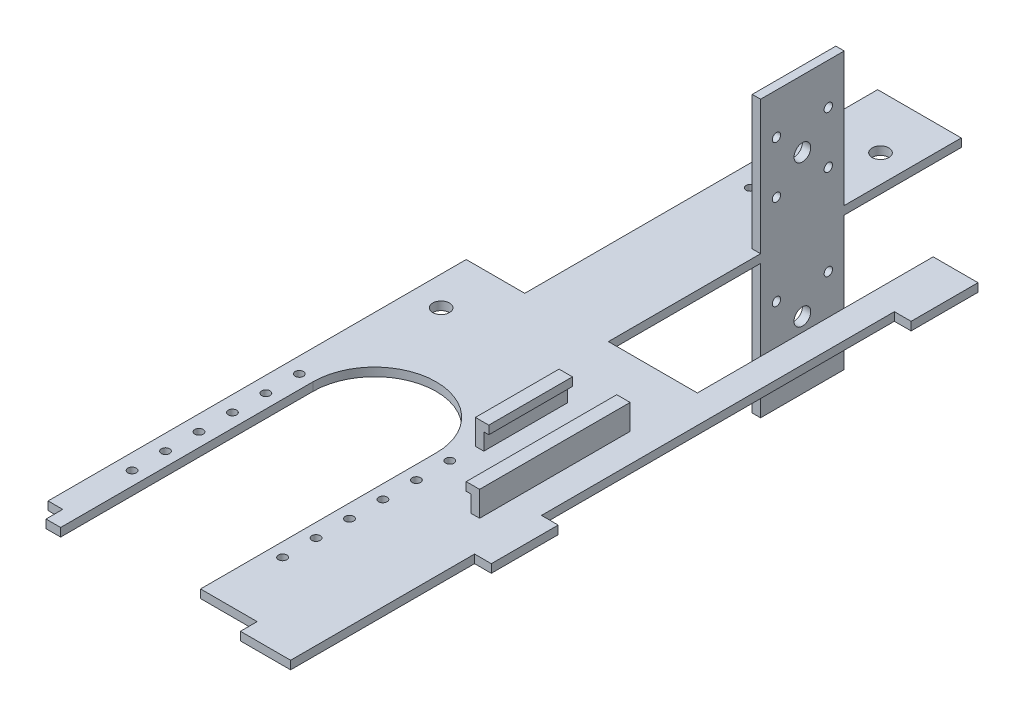
SolidWorks part; units mm, degrees
ref_plane "Front Plane" through (0, 0, 0) normal (0, 0, 1) x (1, 0, 0)
ref_plane "Top Plane" through (0, 0, 0) normal (0, 1, 0) x (1, 0, 0)
ref_plane "Right Plane" through (0, 0, 0) normal (1, 0, 0) x (0, 0, -1)
sketch "Sketch1" plane through (0, 0, 0) normal (0, 0, 1) x (1, 0, 0)
  line L1 (-30, 2.5) -> (30, 2.5)
  line L2 (-30, 2.5) -> (-30, -2.5)
  line L3 (-30, -2.5) -> (30, -2.5)
  line L4 (30, 2.5) -> (30, -2.5)
  line L5 (-30, 2.5) -> (30, -2.5) construction
  line L6 (-30, -2.5) -> (30, 2.5) construction
  point P0 (0, 0)
  dimension "D1" = 60
  dimension "D2" = 5
extrude "Boss-Extrude1" add sketch "Sketch1" along normal blind 391
sketch "Sketch3" plane through (-30, 0, 0) normal (-1, 0, 0) x (0, 0, 1)
  line L0 (391, -2.5) -> (0, -2.5) construction
  line L1 (391, -2.5) -> (141, -2.5)
  line L2 (391, -2.5) -> (391, 2.5)
  line L3 (391, 2.5) -> (141, 2.5)
  line L4 (141, -2.5) -> (141, 2.5)
  line L5 (391, 2.5) -> (391, -2.5) construction
  line L6 (391, 2.5) -> (0, 2.5) construction
  dimension "D1" = 250
extrude "Boss-Extrude2" add sketch "Sketch3" along normal blind 95
sketch "Sketch4" plane through (0, -2.5, 0) normal (0, -1, 0) x (1, 0, 0)
  line L0 (-70.67, 391) -> (-70.67, 250.12) construction
  line L4 (-125, 391) -> (30, 391) construction
  line L5 (-125, 141) -> (-125, 391) construction
  line L6 (-70.67, 391) -> (-70.67, 250.12) construction
  line L7 (-33.84, 391) -> (-33.84, 250.12)
  line L8 (-107.5, 391) -> (-107.5, 250.12)
  line L9 (-125, 250.12) -> (-11.4037, 250.12) construction
  arc A0 (-33.84, 391) -> (-107.5, 391) centre (-70.67, 391) ccw
  arc A1 (-107.5, 250.12) -> (-33.84, 250.12) centre (-70.67, 250.12) ccw
  circle A2 centre (-115.67, 250.12) radius 2.5
  circle A3 centre (-25.67, 250.12) radius 2.5
  circle A4 centre (-25.67, 270.12) radius 2.5
  circle A5 centre (-25.67, 290.12) radius 2.5
  circle A6 centre (-25.67, 310.12) radius 2.5
  circle A7 centre (-25.67, 330.12) radius 2.5
  circle A8 centre (-25.67, 350.12) radius 2.5
  circle A9 centre (-115.67, 270.12) radius 2.5
  circle A10 centre (-115.67, 290.12) radius 2.5
  circle A11 centre (-115.67, 310.12) radius 2.5
  circle A12 centre (-115.67, 330.12) radius 2.5
  circle A13 centre (-115.67, 350.12) radius 2.5
  point P6 (-70.67, 320.56)
  dimension "D3" = 36.83
  dimension "D4" = 5
  dimension "D1" = 54.33
  dimension "D2" = 140.88
  dimension "D5" = 45
  dimension "D8" = 45
  dimension "D6" = 2
  dimension "D7" = 6
extrude "Cut-Extrude1" cut sketch "Sketch4" against normal blind 95
sketch "Sketch5" plane through (0, -2.5, 0) normal (0, -1, 0) x (1, 0, 0)
  line L1 (-125, 141) -> (-30, 141) construction
  line L2 (-40, 141) -> (-90, 141)
  line L3 (-40, 141) -> (-40, 0)
  line L4 (-40, 0) -> (-90, 0)
  line L5 (-90, 141) -> (-90, 0)
  line L6 (-30, 141) -> (-30, 0) construction
  dimension "D1" = 50
  dimension "D2" = 10
extrude "Boss-Extrude3" add sketch "Sketch5" against normal blind 5
sketch "Sketch6" plane through (0, -2.5, 0) normal (0, -1, 0) x (1, 0, 0)
  line L0 (-90, 0) -> (-40, 0) construction
  line L1 (-40, 0) -> (-45, 0)
  line L2 (-40, 0) -> (-40, 50)
  line L3 (-40, 50) -> (-45, 50)
  line L4 (-45, 0) -> (-45, 50)
  line L6 (-40, 0) -> (-40, 141) construction
  dimension "D1" = 50
  dimension "D2" = 5
  dimension "D3" = 0
extrude "Boss-Extrude4" add sketch "Sketch6" along normal blind 80
sketch "Sketch7" plane through (-45, 0, 0) normal (-1, 0, 0) x (0, 0, 1)
  line L0 (50, -42.5) -> (0, -42.5) construction
  line L1 (50, -82.5) -> (50, -2.5) construction
  line L2 (0, -82.5) -> (0, -2.5) construction
  circle A0 centre (25, -42.5) radius 5
  dimension "D1" = 10
extrude "Cut-Extrude2" cut sketch "Sketch7" against normal blind 40
sketch "Sketch8" plane through (0, -2.5, 0) normal (0, -1, 0) x (-1, 0, 0)
  line L0 (30, -141) -> (30, 0) construction
  line L1 (30, -141) -> (0, -141)
  line L2 (30, -141) -> (30, 0)
  line L3 (30, 0) -> (0, 0)
  line L4 (0, -141) -> (-13.214, -141)
  line L5 (30, 0) -> (-30, 0) construction
  line L6 (-13.214, -141) -> (-13.214, 0)
  line L7 (-13.214, 0) -> (0, 0)
extrude "Cut-Extrude3" cut sketch "Sketch8" against normal blind 10
sketch "Sketch11" plane through (30, 0, 0) normal (1, 0, 0) x (0, 0, -1)
  line L0 (-391, -2.5) -> (0, -2.5) construction
  line L1 (0, 2.5) -> (-40, 2.5)
  line L2 (0, 2.5) -> (0, -2.5)
  line L3 (0, -2.5) -> (-40, -2.5)
  line L4 (-40, 2.5) -> (-40, -2.5)
  line L5 (-391, 2.5) -> (0, 2.5) construction
  line L6 (-251, -2.5) -> (-291, -2.5)
  line L7 (-251, -2.5) -> (-251, 2.5)
  line L8 (-251, 2.5) -> (-291, 2.5)
  line L9 (-291, -2.5) -> (-291, 2.5)
  dimension "D1" = 40
  dimension "D2" = 40
  dimension "D3" = 100
extrude "Boss-Extrude5" add sketch "Sketch11" along normal blind 10
sketch "Sketch12" plane through (0, 0, 391) normal (0, 0, 1) x (1, 0, 0)
  line L1 (-33.84, -2.5) -> (30, -2.5) construction
  line L2 (30, 2.5) -> (0, 2.5)
  line L3 (30, 2.5) -> (30, -2.5)
  line L4 (30, -2.5) -> (0, -2.5)
  line L5 (0, 2.5) -> (0, -2.5)
  line L6 (-107.5, -2.5) -> (-125, -2.5)
  line L7 (-107.5, -2.5) -> (-107.5, 2.5)
  line L8 (-107.5, 2.5) -> (-125, 2.5)
  line L9 (-125, -2.5) -> (-125, 2.5)
  dimension "D1" = 30
extrude "Boss-Extrude6" add sketch "Sketch12" along normal blind 10
mirror "Mirror1" about plane through (0, 0, 0) normal (0, 1, 0) of "Cut-Extrude2", "Boss-Extrude4"
ref_plane "Plane3" through (-107.5, 2.5, 401) normal (-1, 0, 0) x (0, 0, 1)
sketch "Sketch14" plane through (0, 0, 401) normal (0, 0, 1) x (1, 0, 0)
  line L0 (-125, -2.5) -> (-107.5, -2.5) construction
  line L1 (-125.25, -2.5) -> (-116.25, -2.5)
  line L2 (-125.25, -2.5) -> (-125.25, 2.5)
  line L3 (-125.25, 2.5) -> (-116.25, 2.5)
  line L4 (-116.25, -2.5) -> (-116.25, 2.5)
  line L5 (-107.5, 2.5) -> (-125, 2.5) construction
  dimension "D1" = 9
extrude "Cut-Extrude4" cut sketch "Sketch14" against normal blind 10
sketch "Sketch15" plane through (0, -2.5, 0) normal (0, -1, 0) x (1, 0, 0)
  line L0 (30, 251) -> (30, 40) construction
  line L1 (13, 271) -> (8, 271)
  line L2 (13, 271) -> (13, 181)
  line L3 (13, 181) -> (8, 181)
  line L4 (8, 271) -> (8, 181)
  line L5 (-33.84, 391) -> (0, 391) construction
  line L6 (-20.5, 185) -> (-25.5, 185)
  line L7 (-20.5, 185) -> (-20.5, 235)
  line L8 (-20.5, 235) -> (-25.5, 235)
  line L9 (-25.5, 185) -> (-25.5, 235)
  line L10 (0, 401) -> (30, 401) construction
  dimension "D1" = 22
  dimension "D2" = 5
  dimension "D3" = 156
  dimension "D4" = 130
  dimension "D5" = 90
  dimension "D6" = 5
  dimension "D7" = 50
  dimension "D8" = 28.5
extrude "Boss-Extrude7" add sketch "Sketch15" along normal blind 15 and the other way blind 20
sketch "Sketch16" plane through (-20.5, 0, 0) normal (1, 0, 0) x (0, 0, -1)
  line L0 (-235, -2.5) -> (-235, -17.5) construction
  line L1 (-185, -17.5) -> (-235, -17.5)
  line L2 (-185, -17.5) -> (-185, -12.5)
  line L3 (-185, -12.5) -> (-235, -12.5)
  line L4 (-235, -17.5) -> (-235, -12.5)
  line L5 (-185, 17.5) -> (-185, 2.5) construction
  line L6 (-235, 17.5) -> (-185, 17.5)
  line L7 (-235, 17.5) -> (-235, 12.5)
  line L8 (-235, 12.5) -> (-185, 12.5)
  line L9 (-185, 17.5) -> (-185, 12.5)
  dimension "D1" = 5
  dimension "D2" = 5
extrude "Boss-Extrude8" add sketch "Sketch16" along normal blind 3
sketch "Sketch18" plane through (8, 0, 0) normal (-1, 0, 0) x (0, 0, 1)
  line L0 (181, 17.5) -> (181, 2.5) construction
  line L1 (271, 17.5) -> (181, 17.5)
  line L2 (271, 17.5) -> (271, 12.5)
  line L3 (271, 12.5) -> (181, 12.5)
  line L4 (181, 17.5) -> (181, 12.5)
  line L5 (271, -2.5) -> (271, -17.5) construction
  line L6 (181, -17.5) -> (271, -17.5)
  line L7 (181, -17.5) -> (181, -12.5)
  line L8 (181, -12.5) -> (271, -12.5)
  line L9 (271, -17.5) -> (271, -12.5)
  dimension "D1" = 5
  dimension "D2" = 5
extrude "Boss-Extrude9" add sketch "Sketch18" along normal blind 3
sketch "Sketch19" plane through (-45, 0, 0) normal (-1, 0, 0) x (0, 0, 1)
  line L0 (0, 0) -> (31.8303, 0) construction
  line L1 (9.5, 27) -> (40.5, 27) construction
  line L2 (9.5, 27) -> (9.5, 58) construction
  line L3 (9.5, 58) -> (40.5, 58) construction
  line L4 (40.5, 27) -> (40.5, 58) construction
  line L5 (9.5, 27) -> (40.5, 58) construction
  line L6 (9.5, 58) -> (40.5, 27) construction
  circle A0 centre (9.5, 58) radius 2.5
  circle A1 centre (40.5, 58) radius 2.5
  circle A2 centre (40.5, 27) radius 2.5
  circle A3 centre (9.5, 27) radius 2.5
  circle A4 centre (40.5, -27) radius 2.5
  circle A5 centre (40.5, -58) radius 2.5
  circle A6 centre (9.5, -58) radius 2.5
  circle A7 centre (9.5, -27) radius 2.5
  point P0 (25, 42.5)
  dimension "D3" = 5
  dimension "D1" = 31
  dimension "D2" = 31
extrude "Cut-Extrude5" cut sketch "Sketch19" against normal blind 28
sketch "Sketch20" plane through (0, 0, 0) normal (0, 0, -1) x (-1, 0, 0)
  line L0 (40, 82.5) -> (40, -82.5) construction
  line L1 (90, -2.5) -> (40, -2.5)
  line L2 (90, -2.5) -> (90, 2.4546)
  line L3 (90, 2.4546) -> (40, 2.4546)
  line L4 (40, -2.5) -> (40, 2.4546)
extrude "Boss-Extrude10" add sketch "Sketch20" along normal blind 70
sketch "Sketch21" plane through (0, -2.5, 0) normal (0, -1, 0) x (1, 0, 0)
  line L0 (-40, -70) -> (-40, 0) construction
  circle A0 centre (-56.5, -38.21) radius 5
  point P5 (-40, -35)
  dimension "D3" = 10
  dimension "D1" = 38.21
  dimension "D2" = 16.5
extrude "Cut-Extrude6" cut sketch "Sketch21" against normal blind 70
sketch "Sketch22" plane through (0, 2.5, 0) normal (0, 1, 0) x (1, 0, 0)
  line L0 (-90, 70) -> (-40, 70) construction
  line L1 (-90, -141) -> (-90, 0) construction
  circle A0 centre (-77.21, -19) radius 2.5
  dimension "D1" = 5
  dimension "D2" = 89
  dimension "D3" = 12.79
extrude "Cut-Extrude7" cut sketch "Sketch22" against normal blind 10
sketch "Sketch23" plane through (0, 2.5, 0) normal (0, 1, 0) x (1, 0, 0)
  line L0 (-107.5, -141) -> (-107.5, -206) construction
  line L1 (-125, -141) -> (-90, -141) construction
  line L2 (-125, -141) -> (-125, -206) construction
  line L3 (-125, -206) -> (-90, -206) construction
  line L4 (-90, -141) -> (-90, -206) construction
  circle A0 centre (-107.5, -173.5) radius 5
  dimension "D3" = 10
  dimension "D1" = 35
  dimension "D2" = 65
extrude "Cut-Extrude8" cut sketch "Sketch23" against normal blind 10
